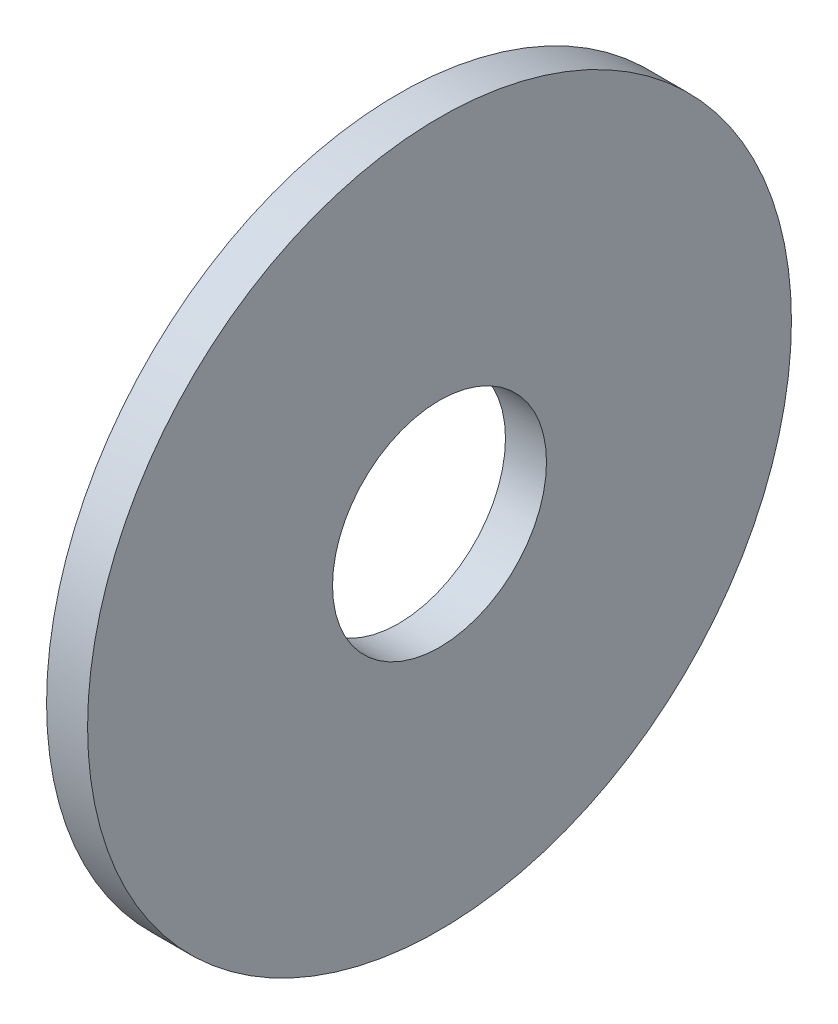
SolidWorks part; units mm, degrees
ref_plane "Front Plane" through (0, 0, 0) normal (0, 0, 1) x (1, 0, 0)
ref_plane "Top Plane" through (0, 0, 0) normal (0, 1, 0) x (1, 0, 0)
ref_plane "Right Plane" through (0, 0, 0) normal (1, 0, 0) x (0, 0, -1)
sketch "Sketch1" plane through (0, 0, 0) normal (1, 0, 0) x (0, 0, -1)
  circle A0 centre (0, 0) radius 11.1125
  circle A1 centre (0, 0) radius 3.3782
  dimension "OD" = 22.225
  dimension "ID" = 6.7564
extrude "Boss-Extrude1" add sketch "Sketch1" along normal blind 1.2954
